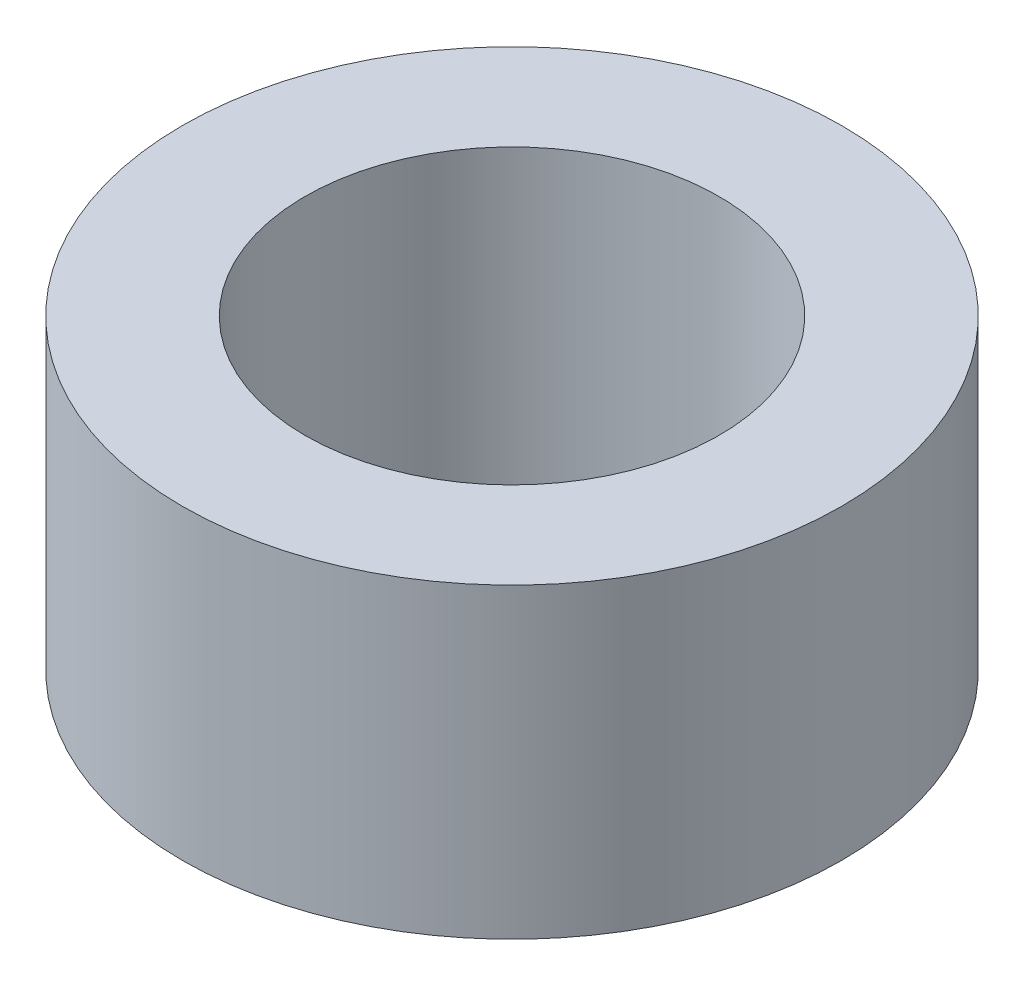
SolidWorks part; units mm, degrees
material "Ti-6Al-2Sn-2Zr-2Mo-2Cr-0.25Si (SS)"
ref_plane "Front Plane" through (0, 0, 0) normal (0, 0, 1) x (1, 0, 0)
ref_plane "Top Plane" through (0, 0, 0) normal (0, 1, 0) x (1, 0, 0)
ref_plane "Right Plane" through (0, 0, 0) normal (1, 0, 0) x (0, 0, -1)
sketch "Sketch1" plane through (0, 0, 0) normal (0, 1, 0) x (1, 0, 0)
  circle A0 centre (0, 0) radius 107.5
  dimension "D1" = 215
extrude "Boss-Extrude1" add sketch "Sketch1" along normal blind 100
sketch "Sketch2" plane through (0, 100, 0) normal (0, 1, 0) x (1, 0, 0)
  circle A0 centre (0, 0) radius 107.5
  circle A1 centre (0, 0) radius 67.5
  dimension "D1" = 135
extrude "Cut-Extrude1" cut sketch "Sketch2" against normal blind 100 contours A1
